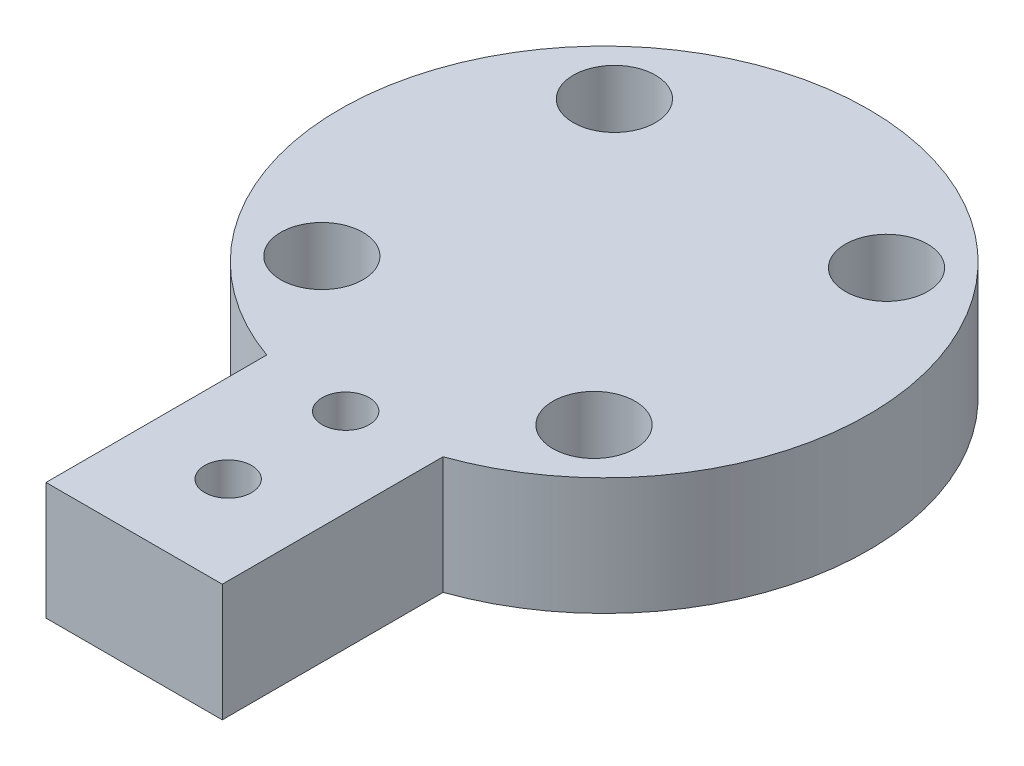
SolidWorks part; units mm, degrees
ref_plane "Front Plane" through (0, 0, 0) normal (0, 0, 1) x (1, 0, 0)
ref_plane "Top Plane" through (0, 0, 0) normal (0, 1, 0) x (1, 0, 0)
ref_plane "Right Plane" through (0, 0, 0) normal (1, 0, 0) x (0, 0, -1)
sketch "Sketch1" plane through (0, 0, 0) normal (0, 1, 0) x (1, 0, 0)
  line L1 (-7.5, 0) -> (7.5, 0)
  line L2 (-7.5, 0) -> (-7.5, -40)
  line L3 (-7.5, -40) -> (7.5, -40)
  line L4 (7.5, 0) -> (7.5, -40)
  circle A0 centre (0, 0) radius 22.5
  dimension "D1" = 45
  dimension "D2" = 15
  dimension "D3" = 40
extrude "Boss-Extrude1" add sketch "Sketch1" along normal blind 10 contours A0 L2 L3 L4 | L4 A0 L2 L1 | L2 A0 L4 L1
sketch "Sketch2" plane through (0, 10, 0) normal (0, 1, 0) x (1, 0, 0)
  circle A0 centre (-11.5793, 12.4466) radius 2
  circle A1 centre (12.4466, 11.5793) radius 2
  circle A2 centre (11.5793, -12.4466) radius 2
  circle A3 centre (-12.4466, -11.5793) radius 2
  point P12 (0, 0)
  dimension "D1" = 4
  dimension "D2" = 17
  dimension "D3" = 4
extrude "Cut-Extrude1" cut sketch "Sketch2" against normal blind 10
sketch "Sketch3" plane through (0, 10, 0) normal (0, 1, 0) x (1, 0, 0)
  line L0 (0, 0) -> (0, -40) construction
  line L1 (-7.5, -40) -> (7.5, -40) construction
  circle A0 centre (0, -22) radius 2
  circle A1 centre (0, -32) radius 2
  dimension "D1" = 4
  dimension "D2" = 4
  dimension "D3" = 8
  dimension "D4" = 10
extrude "Cut-Extrude2" cut sketch "Sketch3" against normal blind 10
sketch "Sketch4" plane through (0, 10, 0) normal (0, 1, 0) x (1, 0, 0)
  circle A0 centre (-11.5793, 12.4466) radius 3.5
  circle A1 centre (12.4466, 11.5793) radius 3.5
  circle A2 centre (11.5793, -12.4466) radius 3.5
  circle A3 centre (-12.4466, -11.5793) radius 3.5
  circle A4 centre (12.4466, 11.5793) radius 2 construction
  point P12 (0, 0)
  dimension "D1" = 7
  dimension "D2" = 4
extrude "Cut-Extrude3" cut sketch "Sketch4" against normal blind 5
